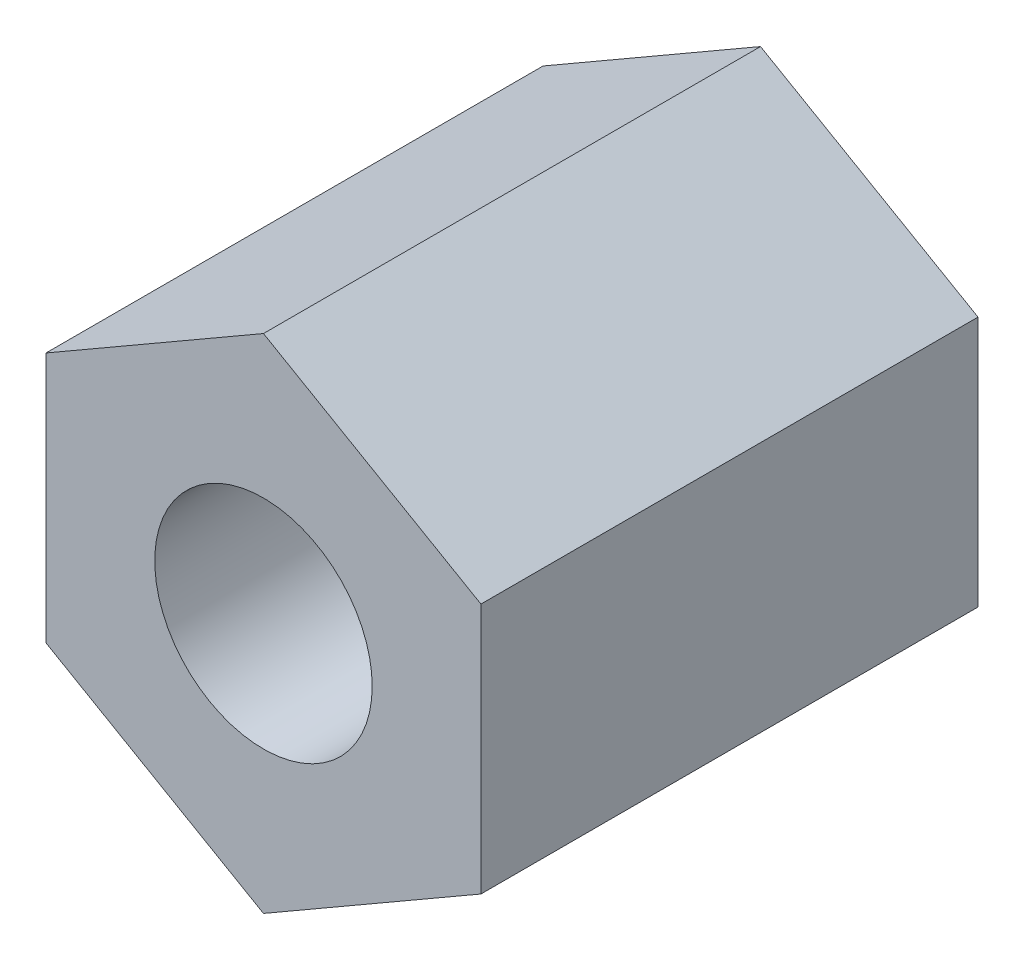
SolidWorks part; units mm, degrees
ref_plane "Face" through (0, 0, 0) normal (0, 0, 1) x (1, 0, 0)
ref_plane "Dessus" through (0, 0, 0) normal (0, 1, 0) x (1, 0, 0)
ref_plane "Droite" through (0, 0, 0) normal (1, 0, 0) x (0, 0, -1)
sketch "Esquisse1" plane through (0, 0, 0) normal (0, 0, 1) x (1, 0, 0)
  line L0 (3.5, -2.0207) -> (3.5, 2.0207)
  line L1 (3.5, 2.0207) -> (0, 4.0415)
  line L2 (-3.5, 0) -> (3.5, 0) construction
  line L3 (0, -4.0415) -> (0, 4.0415) construction
  line L4 (3.5, -2.0207) -> (0, -4.0415)
  line L5 (-3.5, -2.0207) -> (0, -4.0415)
  line L6 (-3.5, 2.0207) -> (0, 4.0415)
  line L7 (-3.5, -2.0207) -> (-3.5, 2.0207)
  circle A0 centre (0, 0) radius 1.75
  point P8 (0, 0)
  dimension "D3" = 3.5
  dimension "D1" = 120
  dimension "D2" = 7
extrude "Boss.-Extru.1" add sketch "Esquisse1" along normal blind 8
